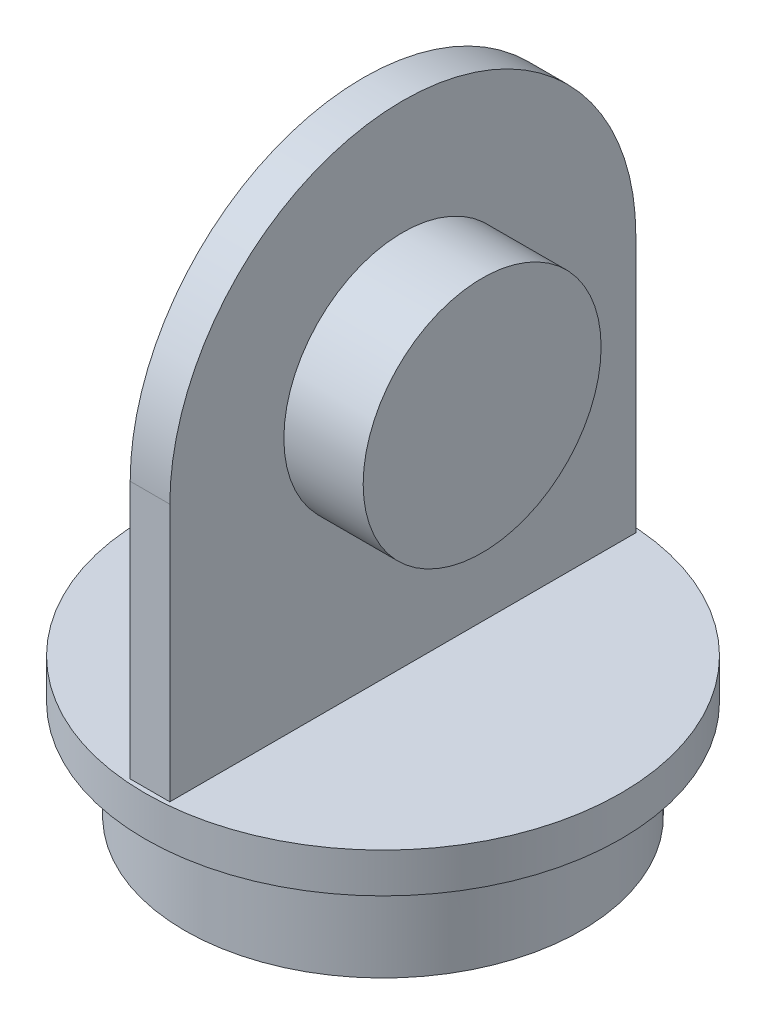
SolidWorks part; units mm, degrees
ref_plane "Front Plane" through (0, 0, 0) normal (0, 0, 1) x (1, 0, 0)
ref_plane "Top Plane" through (0, 0, 0) normal (0, 1, 0) x (1, 0, 0)
ref_plane "Right Plane" through (0, 0, 0) normal (1, 0, 0) x (0, 0, -1)
sketch "Sketch1" plane through (0, 0, 0) normal (0, 1, 0) x (1, 0, 0)
  circle A0 centre (0, 0) radius 12
  dimension "D1" = 24
extrude "Boss-Extrude1" add sketch "Sketch1" along normal blind 2
sketch "Sketch2" plane through (0, 0, 0) normal (1, 0, 0) x (0, 0, -1)
  line L0 (-11.75, 2) -> (-11.75, 15)
  line L1 (11.75, 15) -> (11.75, 2)
  line L2 (-11.75, 2) -> (11.75, 2)
  arc A0 (-11.75, 15) -> (11.75, 15) centre (0, 15) cw
  dimension "D1" = 13
  dimension "D2" = 0.25
  dimension "D3" = 0.25
extrude "Boss-Extrude2" add sketch "Sketch2" along normal mid plane 2
sketch "Sketch3" plane through (0, 0, 0) normal (0, -1, 0) x (1, 0, 0)
  circle A0 centre (0, 0) radius 10
  dimension "D1" = 20
extrude "Boss-Extrude3" add sketch "Sketch3" along normal blind 5
sketch "Sketch4" plane through (0, 0, 0) normal (1, 0, 0) x (0, 0, -1)
  circle A0 centre (0, 15) radius 6
  arc A1 (11.75, 15) -> (-11.75, 15) centre (0, 15) ccw construction
  dimension "D1" = 12
extrude "Boss-Extrude4" add sketch "Sketch4" along normal mid plane 10
scale "Scale1" bodies to scale 104 scale about centroid uniform scaling yes scale factor 2
